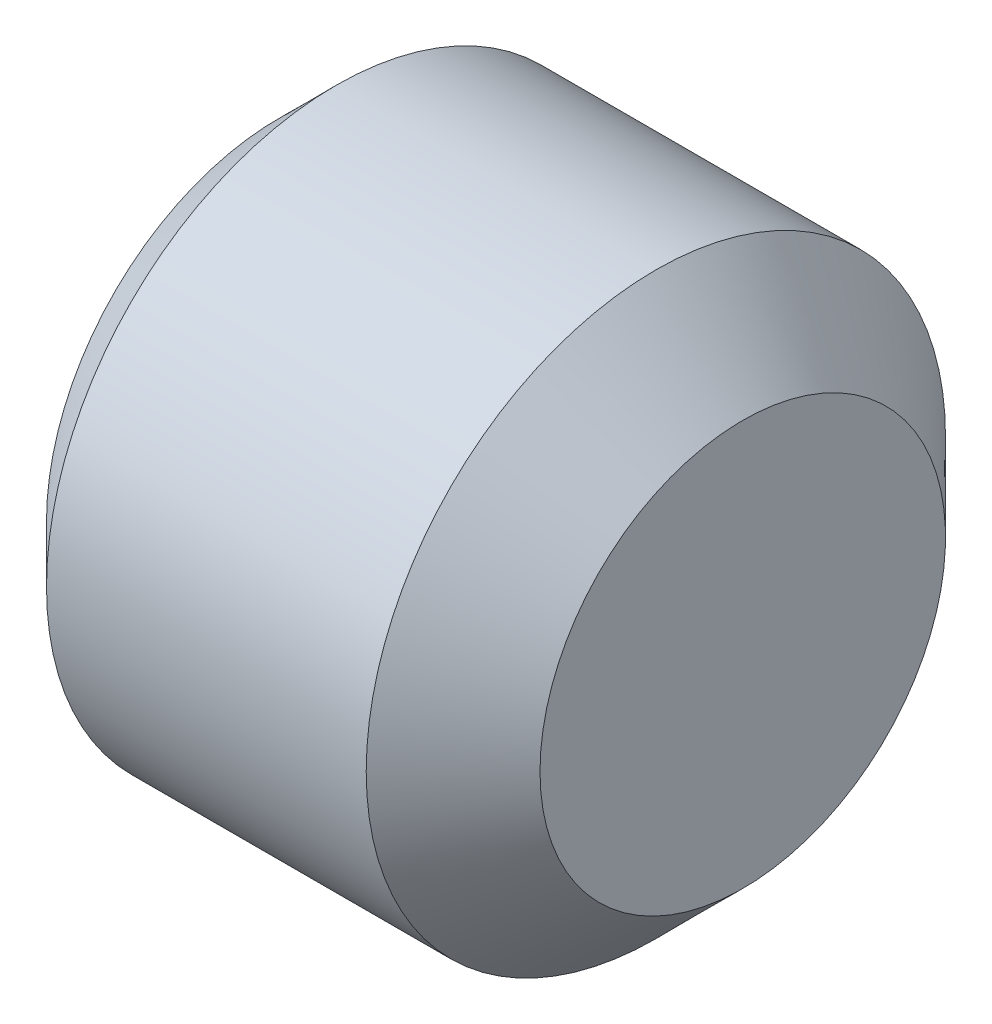
SolidWorks part; units mm, degrees
ref_plane "正面" through (0, 0, 0) normal (0, 0, 1) x (1, 0, 0)
ref_plane "平面" through (0, 0, 0) normal (0, 1, 0) x (1, 0, 0)
ref_plane "右側面" through (0, 0, 0) normal (1, 0, 0) x (0, 0, -1)
ref_plane "平面1" through (0, 0, 0) normal (0, 0, 1) x (1, 0, 0)
sketch "ｽｹｯﾁ1" plane through (0, 0, 0) normal (0, 0, 1) x (1, 0, 0)
  line L0 (-4, 0) -> (-4, 2.0095)
  line L1 (-4, 2.0095) -> (-3.5095, 2.5)
  line L2 (-3.5095, 2.5) -> (-0.75, 2.5)
  line L3 (-0.75, 2.5) -> (0, 1.75)
  line L4 (0, 1.75) -> (0, 0)
  line L5 (0, 0) -> (-4, 0)
  line L6 (0, 0) -> (-4, 0) construction
revolve "回転1" add sketch "ｽｹｯﾁ1" angle 360 about L6
cosmetic thread "ねじ山1" parameters "D1"=4, "D2"=4.019
ref_plane "平面2" through (-4, 0, 0) normal (-1, 0, 0) x (0, 0, 1)
sketch "ｽｹｯﾁ2" plane through (-4, 0, 0) normal (-1, 0, 0) x (0, 0, 1)
  line L0 (0.7217, -1.25) -> (1.4434, 0)
  line L1 (1.4434, 0) -> (0.7217, 1.25)
  line L2 (0.7217, 1.25) -> (-0.7217, 1.25)
  line L3 (-0.7217, 1.25) -> (-1.4434, 0)
  line L4 (-1.4434, 0) -> (-0.7217, -1.25)
  line L5 (-0.7217, -1.25) -> (0.7217, -1.25)
extrude "ｶｯﾄ - 押し出し1" cut sketch "ｽｹｯﾁ2" against normal blind 2
ref_plane "平面3" through (0, 0, 0) normal (0, 0, 1) x (1, 0, 0)
sketch "ｽｹｯﾁ3" plane through (0, 0, 0) normal (0, 0, 1) x (1, 0, 0)
  line L0 (-2, 0) -> (-2, 1.25)
  line L1 (-2, 1.25) -> (-1.2783, 0)
  line L2 (-1.2783, 0) -> (-2, 0)
  line L3 (-1.2783, 0) -> (-2, 0) construction
revolve "ｶｯﾄ - 回転1" cut sketch "ｽｹｯﾁ3" angle 360 about L3
